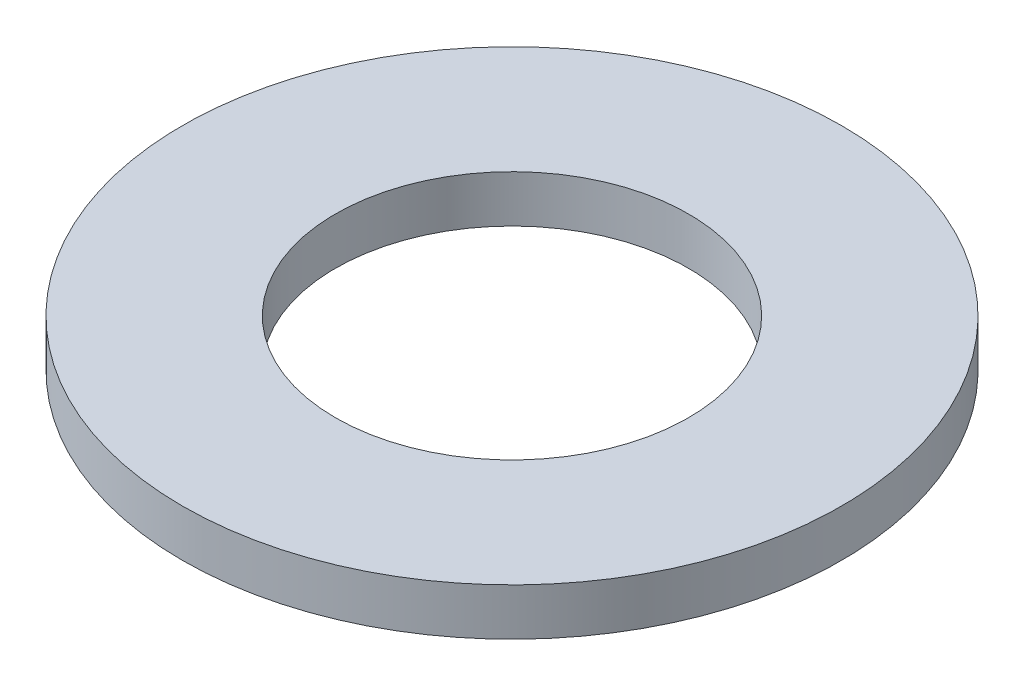
SolidWorks part; units mm, degrees
ref_plane "Front Plane" through (0, 0, 0) normal (0, 0, 1) x (1, 0, 0)
ref_plane "Top Plane" through (0, 0, 0) normal (0, 1, 0) x (1, 0, 0)
ref_plane "Right Plane" through (0, 0, 0) normal (1, 0, 0) x (0, 0, -1)
sketch "Sketch1" plane through (0, 0, 0) normal (0, 1, 0) x (1, 0, 0)
  circle A0 centre (0, 0) radius 14
  circle A1 centre (0, 0) radius 7.5
  dimension "D1" = 15
  dimension "D2" = 28
extrude "Boss-Extrude1" add sketch "Sketch1" along normal blind 2
